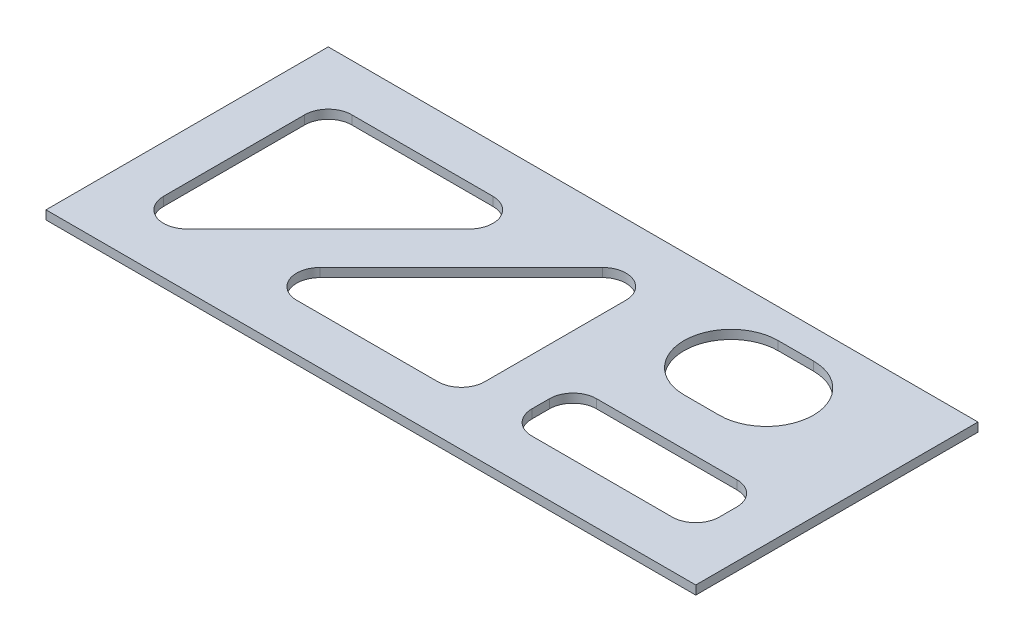
SolidWorks part; units mm, degrees
material "ASTM A36 Steel"
ref_plane "Front Plane" through (0, 0, 0) normal (0, 0, 1) x (1, 0, 0)
ref_plane "Top Plane" through (0, 0, 0) normal (0, 1, 0) x (1, 0, 0)
ref_plane "Right Plane" through (0, 0, 0) normal (1, 0, 0) x (0, 0, -1)
sketch "Sketch1" plane through (0, 0, 0) normal (0, 1, 0) x (1, 0, 0)
  line L1 (175.4187, 76.2) -> (-175.4187, 76.2)
  line L2 (175.4187, 76.2) -> (175.4188, -76.2)
  line L3 (175.4188, -76.2) -> (-175.4187, -76.2)
  line L4 (-175.4187, 76.2) -> (-175.4187, -76.2)
  line L5 (175.4187, 76.2) -> (-175.4187, -76.2) construction
  line L6 (175.4188, -76.2) -> (-175.4187, 76.2) construction
  point P0 (0, 0)
  dimension "D1" = 152.4
  dimension "D2" = 350.8375
extrude "Boss-Extrude1" add sketch "Sketch1" along normal mid plane 4.7625
sketch "Sketch2" plane through (0, 2.3813, 0) normal (0, 1, 0) x (1, 0, 0)
  line L0 (102.3938, 34.925) -> (83.3438, 34.925) construction
  line L1 (102.3938, 9.525) -> (83.3438, 9.525)
  line L2 (102.3938, 60.325) -> (83.3438, 60.325)
  line L4 (175.4188, -76.2) -> (175.4187, 76.2) construction
  line L5 (175.4187, 76.2) -> (-175.4187, 76.2) construction
  line L6 (-137.3187, 50.8) -> (-61.1188, 50.8)
  line L7 (-52.1385, 29.1197) -> (-128.3385, -47.0803)
  line L8 (-150.0187, -38.1) -> (-150.0187, 38.1)
  line L9 (-175.4187, 76.2) -> (-175.4187, -76.2) construction
  line L10 (-65.4767, -50.8) -> (10.7233, -50.8)
  line L11 (23.4233, -38.1) -> (23.4233, 38.1)
  line L12 (1.743, 47.0803) -> (-74.457, -29.1197)
  line L13 (-175.4187, -76.2) -> (175.4188, -76.2) construction
  line L14 (61.5233, -50.8) -> (137.3188, -50.8)
  line L15 (150.0188, -38.1) -> (150.0188, -28.575)
  line L16 (137.3188, -15.875) -> (61.5233, -15.875)
  line L17 (48.8233, -28.575) -> (48.8233, -38.1)
  arc A0 (102.3938, 9.525) -> (102.3938, 60.325) centre (102.3938, 34.925) ccw
  arc A1 (83.3438, 60.325) -> (83.3438, 9.525) centre (83.3438, 34.925) ccw
  arc A2 (-61.1188, 50.8) -> (-52.1385, 29.1197) centre (-61.1188, 38.1) cw
  arc A3 (-128.3385, -47.0803) -> (-150.0187, -38.1) centre (-137.3187, -38.1) cw
  arc A4 (-150.0187, 38.1) -> (-137.3187, 50.8) centre (-137.3187, 38.1) cw
  arc A5 (10.7233, -50.8) -> (23.4233, -38.1) centre (10.7233, -38.1) ccw
  arc A6 (23.4233, 38.1) -> (1.743, 47.0803) centre (10.7233, 38.1) ccw
  arc A7 (-74.457, -29.1197) -> (-65.4767, -50.8) centre (-65.4767, -38.1) ccw
  arc A8 (137.3188, -50.8) -> (150.0188, -38.1) centre (137.3188, -38.1) ccw
  arc A9 (150.0188, -28.575) -> (137.3188, -15.875) centre (137.3188, -28.575) ccw
  arc A10 (61.5233, -15.875) -> (48.8233, -28.575) centre (61.5233, -28.575) ccw
  arc A11 (48.8233, -38.1) -> (61.5233, -50.8) centre (61.5233, -38.1) ccw
  point P2 (92.8688, 34.925)
  point P31 (-137.3188, -50.8)
  point P32 (10.7233, 50.8)
  dimension "D2" = 25.4
  dimension "D7" = 12.7
  dimension "D9" = 25.4
  dimension "D1" = 19.05
  dimension "D3" = 41.275
  dimension "D4" = 82.55
  dimension "D5" = 25.4
  dimension "D6" = 25.4
  dimension "D8" = 45
  dimension "D10" = 25.4
  dimension "D11" = 25.4
  dimension "D12" = 25.4
  dimension "D13" = 25.4
extrude "Cut-Extrude1" cut sketch "Sketch2" against normal through all
